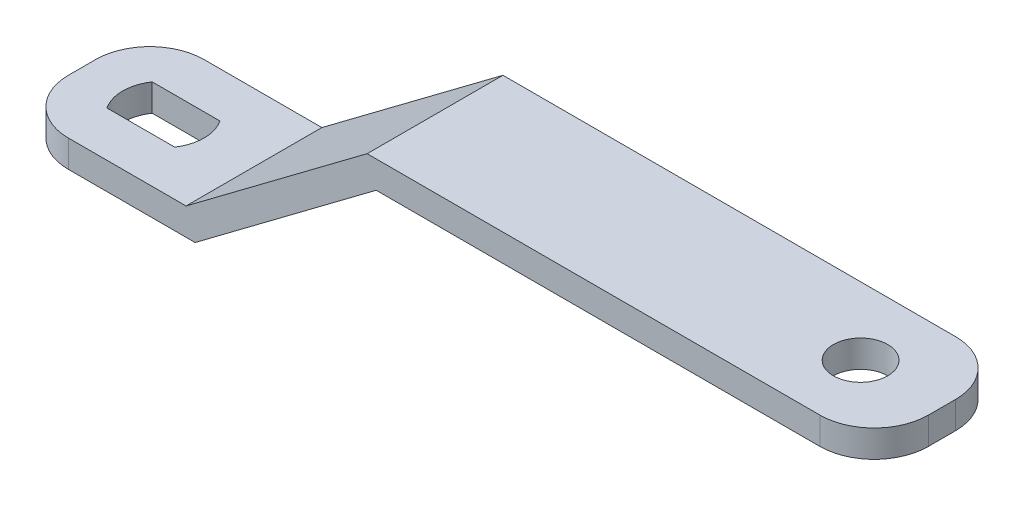
SolidWorks part; units mm, degrees
ref_plane "Plan de face" through (0, 0, 0) normal (0, 0, 1) x (1, 0, 0)
ref_plane "Plan de dessus" through (0, 0, 0) normal (0, 1, 0) x (1, 0, 0)
ref_plane "Plan de droite" through (0, 0, 0) normal (1, 0, 0) x (0, 0, -1)
sketch "Esquisse1" plane through (0, 0, 0) normal (0, 0, 1) x (1, 0, 0)
  line L0 (0, 0) -> (20, 0)
  line L1 (20, 0) -> (40, 15)
  line L2 (40, 15) -> (95, 15)
  line L3 (95, 15) -> (95, 18)
  line L4 (95, 18) -> (39, 18)
  line L5 (39, 18) -> (19, 3)
  line L6 (19, 3) -> (0, 3)
  line L7 (0, 3) -> (0, 0)
  dimension "D1" = 3
  dimension "D2" = 3
  dimension "D3" = 3
  dimension "D4" = 20
  dimension "D5" = 55
  dimension "D6" = 95
  dimension "D7" = 15
extrude "Boss.-Extru.1" add sketch "Esquisse1" along normal blind 15
sketch "Esquisse3" plane through (0, 18, 0) normal (0, 1, 0) x (1, 0, 0)
  line L0 (5.2583, -5) -> (12.7417, -5)
  line L1 (6, 0) -> (89, 0)
  line L2 (0, -6) -> (0, -9)
  line L3 (6, -15) -> (89, -15)
  line L4 (95, -6) -> (95, -9)
  line L5 (5.2583, -10) -> (12.7417, -10)
  arc A0 (89, -15) -> (95, -9) centre (89, -9) ccw
  arc A1 (89, 0) -> (95, -6) centre (89, -6) cw
  arc A2 (0, -9) -> (6, -15) centre (6, -9) ccw
  arc A3 (6, 0) -> (0, -6) centre (6, -6) ccw
  circle A4 centre (86, -7.5) radius 3
  arc A5 (5.2583, -5) -> (5.2583, -10) centre (9, -7.5) ccw
  arc A6 (12.7417, -10) -> (12.7417, -5) centre (9, -7.5) ccw
  point P8 (95, -15)
  point P15 (0, 0)
  point P18 (0, -7.5)
  point P20 (95, -7.5)
  dimension "D1" = 6
  dimension "D2" = 6
  dimension "D4" = 9
  dimension "D3" = 9
  dimension "D5" = 9
  dimension "D6" = 5
  dimension "D7" = 2.5
extrude "Enlèv. mat.-Extru.1" cut sketch "Esquisse3" against normal through all flip side to cut
